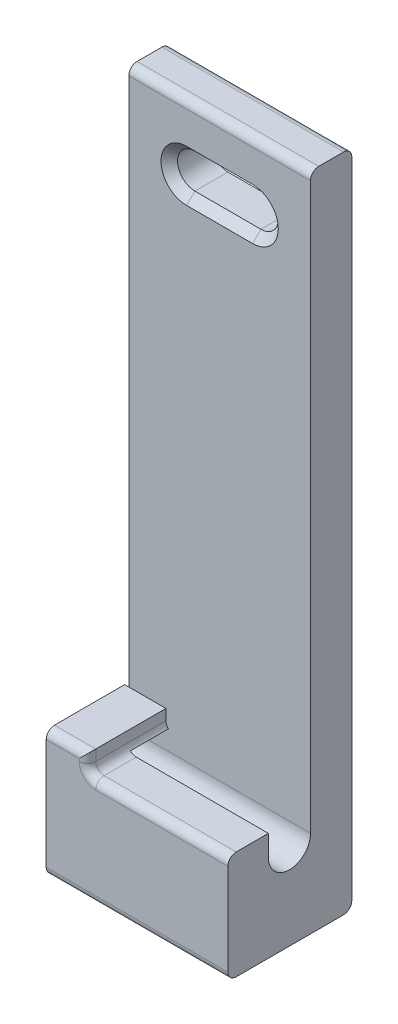
SolidWorks part; units mm, degrees
ref_plane "Front Plane" through (0, 0, 0) normal (0, 0, 1) x (1, 0, 0)
ref_plane "Top Plane" through (0, 0, 0) normal (0, 1, 0) x (1, 0, 0)
ref_plane "Right Plane" through (0, 0, 0) normal (1, 0, 0) x (0, 0, -1)
sketch "Sketch1" plane through (0, 0, 0) normal (1, 0, 0) x (0, 0, -1)
  line L1 (0, 0) -> (-15, 0)
  line L2 (0, 0) -> (0, 80)
  line L3 (0, 80) -> (-15, 80)
  line L4 (-15, 0) -> (-15, 80)
  line L5 (0, 0) -> (-15, 80) construction
  line L6 (0, 80) -> (-15, 0) construction
  point P4 (-7.5, 40)
  dimension "D1" = 15
  dimension "D2" = 80
extrude "Boss-Extrude1" add sketch "Sketch1" along normal blind 22
sketch "Sketch2" plane through (22, 0, 0) normal (1, 0, 0) x (0, 0, -1)
  line L1 (-15, 80) -> (-15, 0) construction
  line L3 (0, 0) -> (0, 80) construction
  line L4 (-15, 13.1) -> (-10.1, 13.1)
  line L5 (-10.1, 13.1) -> (-10.1, 10.55)
  line L8 (-5, 10.55) -> (-5, 80)
  line L9 (0, 80) -> (-15, 80) construction
  line L10 (-5, 80) -> (-15, 80)
  line L11 (-15, 80) -> (-15, 13.1)
  line L12 (-15, 0) -> (0, 0) construction
  arc A0 (-10.1, 10.55) -> (-5, 10.55) centre (-7.55, 10.55) ccw
  arc A1 (-5, 10.55) -> (-10.1, 10.55) centre (-7.55, 10.55) ccw construction
  point P1 (-7.55, 8)
  point P6 (-7.55, 13.1)
  line M5 (0, 80) -> (-15, 80)
  line M6 (-15, 80) -> (-15, 0)
  dimension "D4" = 2.55
  dimension "D1" = 8
  dimension "D3" = 5
extrude "Cut-Extrude1" cut sketch "Sketch2" against normal through all contours L5 A0 L8 L4 M5 M6
sketch "Sketch3" plane through (0, 0, 5) normal (0, 0, 1) x (1, 0, 0)
  line L0 (11, 80) -> (11, 72) construction
  line L1 (0, 80) -> (22, 80) construction
  line L2 (7, 72) -> (15, 72) construction
  line L3 (7, 74.1) -> (15, 74.1)
  line L4 (7, 69.9) -> (15, 69.9)
  line L5 (0, 10.55) -> (0, 80) construction
  arc A0 (7, 74.1) -> (7, 69.9) centre (7, 72) ccw
  arc A1 (15, 69.9) -> (15, 74.1) centre (15, 72) ccw
  point P6 (11, 72)
  point P11 (15, 54.6428)
  dimension "D1" = 8
  dimension "D2" = 4.2
  dimension "D3" = 7
extrude "Cut-Extrude2" cut sketch "Sketch3" against normal through all
chamfer "Chamfer1" distance 1 angle 45 4 edges at (11, 69.9, 5) (17.1, 72, 5) (4.9, 72, 5) (11, 74.1, 5)
fillet "Fillet1" [suppressed] radius 1
sketch "Sketch6" plane through (0, 0, 0) normal (-1, 0, 0) x (0, 0, 1)
  line L0 (10.1, 13.1) -> (10.1, 10.55) construction
  line L1 (15, 13.1) -> (10.1, 13.1)
  line L2 (15, 13.1) -> (15, 13.4)
  line L3 (15, 13.4) -> (10.1, 13.4)
  line L4 (10.1, 13.1) -> (10.1, 13.4)
  line L5 (15, 13.1) -> (10.1, 13.4) construction
  line L6 (15, 13.4) -> (10.1, 13.1) construction
  line L7 (15, 13.4) -> (5.5, 13.4)
  line L8 (15, 13.4) -> (15, 15.4)
  line L9 (15, 15.4) -> (5.5, 15.4)
  line L10 (5.5, 13.4) -> (5.5, 15.4)
  line L11 (15, 13.4) -> (5.5, 15.4) construction
  line L12 (15, 15.4) -> (5.5, 13.4) construction
  line L13 (5, 10.55) -> (5, 80) construction
  circle A0 centre (7.55, 10.55) radius 2.55 construction
  arc A1 (5, 10.55) -> (10.1, 10.55) centre (7.55, 10.55) ccw construction
  point P9 (12.55, 13.25)
  point P14 (10.25, 14.4)
  line M11 (15, 13.1) -> (10.1, 13.1)
  dimension "D1" = 0.3
  dimension "D2" = 2
  dimension "D3" = 0.5
extrude "Boss-Extrude2" add sketch "Sketch6" against normal blind 5 contours L10 L7 L3 L8 L9 | L4 L2 L3 M11
fillet "Fillet2" radius 1 8 edges at (5, 14.25, 15) (11, 0, 0) (11, 80, 0) (11, 80, 5) (13.5, 13.1, 15) (11, 0, 15) (2.5, 15.4, 15) (5, 13.1, 12.55)
